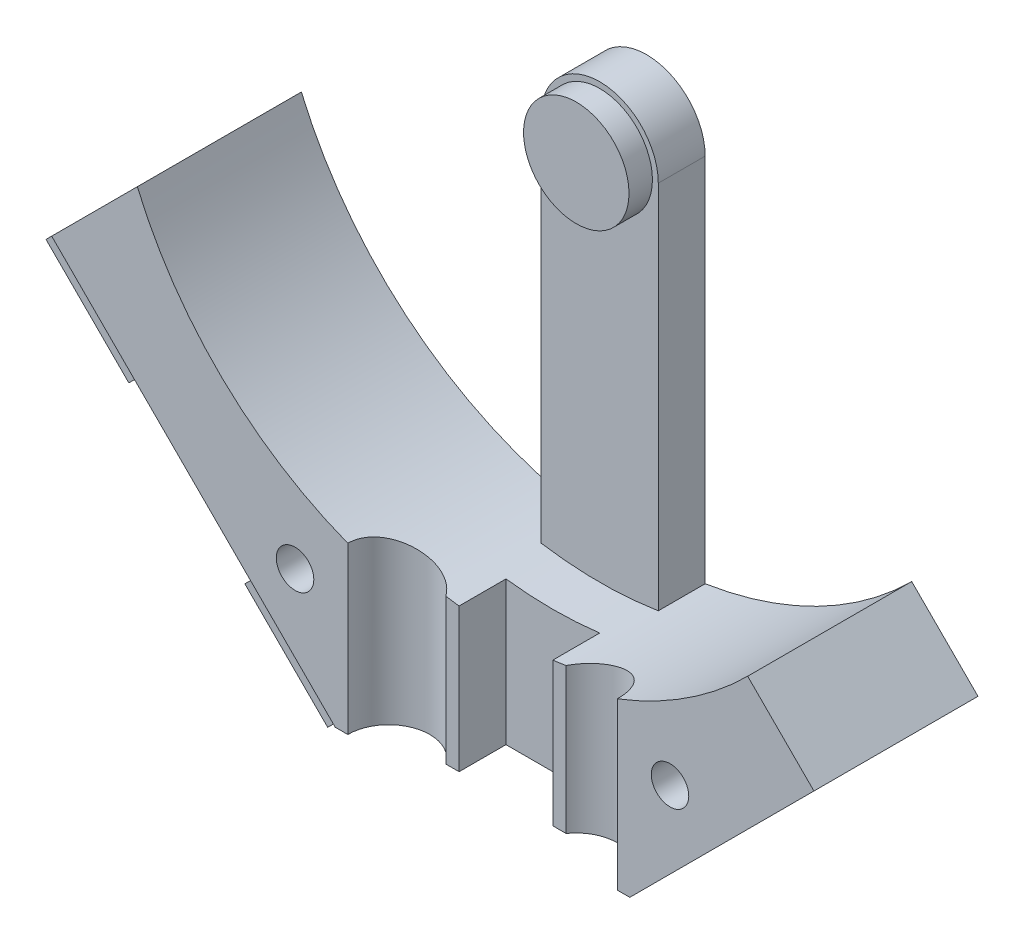
SolidWorks part; units mm, degrees
ref_plane "Front Plane" through (0, 0, 0) normal (0, 0, 1) x (1, 0, 0)
ref_plane "Top Plane" through (0, 0, 0) normal (0, 1, 0) x (1, 0, 0)
ref_plane "Right Plane" through (0, 0, 0) normal (1, 0, 0) x (0, 0, -1)
sketch "Sketch1" plane through (0, 0, 0) normal (0, 0, 1) x (1, 0, 0)
  line L0 (14.1421, -14.1421) -> (11.3137, -11.3137)
  line L1 (-6.4437, -22) -> (6.2843, -22)
  line L2 (-22.6274, -14.1421) -> (-14.7307, -6.2454)
  line L3 (6.2843, -22) -> (14.1421, -14.1421)
  line L5 (-6.4437, -22) -> (-10.6066, -26.163)
  line L14 (-19.0919, -17.6777) -> (-22.6274, -14.1421)
  line L15 (-14.8492, -13.435) -> (-19.0919, -17.6777)
  line L18 (-9.8995, -18.3848) -> (-14.8492, -13.435)
  line L20 (-14.1421, -22.6274) -> (-9.8995, -18.3848)
  line L21 (-10.6066, -26.163) -> (-14.1421, -22.6274)
  arc A1 (11.3137, -11.3137) -> (-14.7307, -6.2454) centre (0, 0) cw
extrude "Boss-Extrude1" add sketch "Sketch1" along normal blind 7
sketch "Sketch2" plane through (0, 0, 0) normal (0, 0, 1) x (1, 0, 0)
  line L0 (0, 0) -> (0, -16) construction
  line L1 (0, 0) -> (2.5, 0) construction
  line L2 (0, 0) -> (-2.5, 0) construction
  line L3 (-2.5, 0) -> (-2.5, -22)
  line L5 (-2.5, -22) -> (2.5, -22)
  line L6 (2.5, -22) -> (2.5, 0)
  arc A1 (2.5, 0) -> (-2.5, 0) centre (0, 0) ccw
extrude "Boss-Extrude2" add sketch "Sketch2" along normal blind 2
sketch "Sketch3" plane through (0, 0, 0) normal (0, 0, 1) x (1, 0, 0)
  line L0 (0, 0) -> (0, 0.925) construction
  circle A1 centre (0, 0) radius 2.25
extrude "Boss-Extrude3" add sketch "Sketch3" along normal blind 1 from offset 2
sketch "Sketch6" plane through (0, 0, 0) normal (0, 1, 0) x (1, 0, 0)
  line L0 (0, -7) -> (4, -7) construction
  line L2 (0, -7) -> (-4, -7) construction
  line L3 (0, -7) -> (-4, -7) construction
  line L7 (0, -7) -> (4, -7) construction
  circle A0 centre (-4, -7) radius 1.75
  circle A1 centre (4, -7) radius 1.75
extrude "Cable Tubes" cut sketch "Sketch6" along normal blind 20 from offset 22.5 offset against normal yes
sketch "Sketch7" plane through (0, 0, 0) normal (0, 1, 0) x (1, 0, 0)
  line L0 (-3, -7) -> (3, -7)
  line L1 (-3, -6) -> (-2, -6)
  line L2 (-2, -6) -> (-2, -4)
  line L3 (-2, -4) -> (2, -4)
  line L4 (2, -4) -> (2, -6)
  line L5 (2, -6) -> (3, -6)
  line L6 (3, -7) -> (3, -6)
  line L8 (-3, -6) -> (-3, -7)
extrude "Wire Canals" cut sketch "Sketch7" along normal blind 8 from offset 22.5 offset against normal yes
sketch "Sketch4" plane through (0, 0, 0) normal (0, 0, 1) x (1, 0, 0)
  line L0 (0, -17) -> (-8, -17) construction
  line L1 (0, -16) -> (0, -17) construction
  line L2 (0, -17) -> (8, -17) construction
  line L3 (-11.3186, -23.3297) -> (-9.1973, -21.2083) construction
  line L4 (-9.1973, -21.2083) -> (-17.6826, -12.7231) construction
  line L7 (-17.6826, -12.7231) -> (-19.8039, -14.8444) construction
  circle A0 centre (-11.3186, -23.3297) radius 0.8
  circle A1 centre (-17.6826, -12.7231) radius 0.8
  circle A2 centre (8, -17) radius 0.8
  circle A3 centre (-9.1973, -21.2083) radius 0.8
  circle A4 centre (-8, -17) radius 0.8
  circle A6 centre (-19.8039, -14.8444) radius 0.8
extrude "Screw Holes" cut sketch "Sketch4" along normal through all
sketch "Sketch10" plane through (0, 0, 0) normal (0, 0, 1) x (1, 0, 0)
  line L0 (-19.0919, -17.6777) -> (-14.8492, -13.435)
  line L1 (-14.8492, -13.435) -> (-18.3848, -9.8995)
  line L3 (-18.3848, -9.8995) -> (-22.6274, -14.1421)
  line L4 (-22.6274, -14.1421) -> (-19.0919, -17.6777)
  line L5 (-14.1421, -22.6274) -> (-9.8995, -18.3848)
  line L6 (-9.8995, -18.3848) -> (-6.2843, -22)
  line L8 (-6.2843, -22) -> (-6.4437, -22)
  line L9 (-6.4437, -22) -> (-10.6066, -26.163)
  line L10 (-10.6066, -26.163) -> (-14.1421, -22.6274)
extrude "Cut-Extrude2" cut sketch "Sketch10" along normal blind 4 from offset 3
